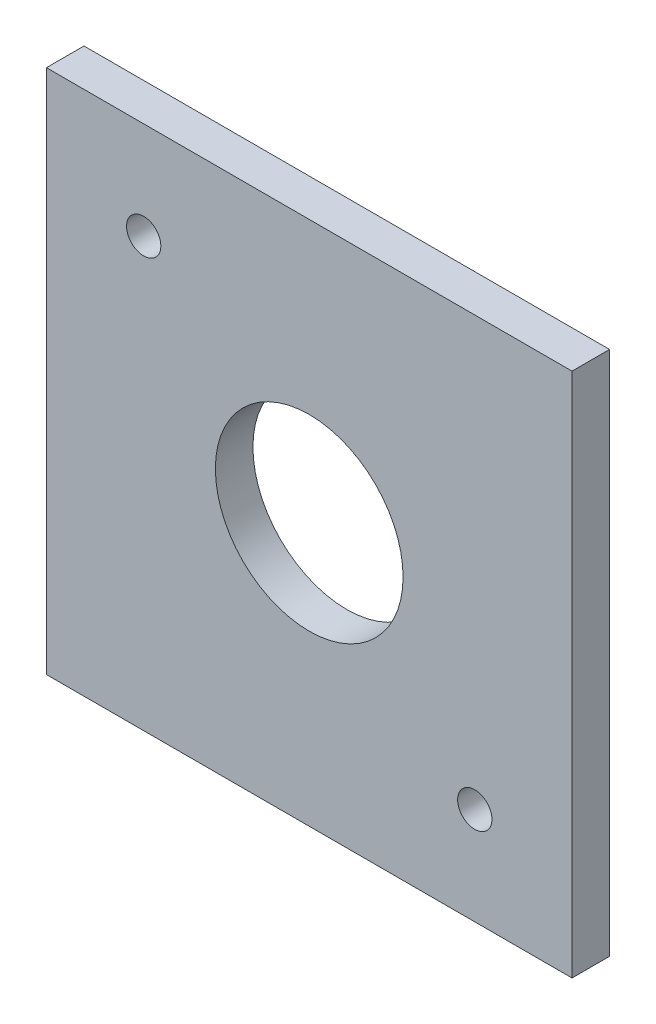
SolidWorks part; units mm, degrees
material "PET"
ref_plane "Front" through (0, 0, 0) normal (0, 0, 1) x (1, 0, 0)
ref_plane "Top" through (0, 0, 0) normal (0, 1, 0) x (1, 0, 0)
ref_plane "Right" through (0, 0, 0) normal (1, 0, 0) x (0, 0, -1)
sketch "Sketch1" plane through (0, 0, 0) normal (0, 0, 1) x (1, 0, 0)
  line L1 (-22.225, -22.225) -> (22.225, -22.225)
  line L2 (-22.225, -22.225) -> (-22.225, 22.225)
  line L3 (-22.225, 22.225) -> (22.225, 22.225)
  line L4 (22.225, -22.225) -> (22.225, 22.225)
  line L5 (-22.225, -22.225) -> (22.225, 22.225) construction
  line L6 (-22.225, 22.225) -> (22.225, -22.225) construction
  point P0 (0, 0)
  dimension "D1" = 44.45
extrude "Boss-Extrude1" add sketch "Sketch1" along normal blind 3.175
sketch "Sketch4" plane through (0, 0, 3.175) normal (0, 0, 1) x (1, 0, 0)
  line L0 (-14, 14) -> (14, 14) construction
  line L1 (14, 14) -> (14, -14) construction
  line L3 (14, -14) -> (-14, -14) construction
  line L4 (-14, -14) -> (-14, 14) construction
  line L6 (0, 14) -> (0, 22.225) construction
  line L7 (22.225, 22.225) -> (-22.225, 22.225) construction
  line L9 (14, 0) -> (22.225, 0) construction
  line L10 (22.225, -22.225) -> (22.225, 22.225) construction
  point P0 (-14, 14)
  point P2 (14, -14)
  dimension "D1" = 28
hole_wizard "M2.5 Clearance Hole1" positions "Sketch4" profile "Sketch3" hole size "M2.5" standard "ANSI Metric" end condition through all
sketch "Sketch3" plane through (-14, 14, 3.175) normal (1, 0, 0) x (0, -1, 0)
  line L0 (0, 0) -> (0, 3.175)
  line L1 (0, 3.175) -> (1.45, 3.175)
  line L2 (1.45, 3.175) -> (1.45, 0)
  line L5 (1.45, 0) -> (0, 0)
  line L11 (0, -6.35) -> (0, 107.95) construction
  dimension "Thru Hole Dia." = 2.9
  dimension "Thru Hole Depth" = 3.175
sketch "Sketch5" plane through (0, 0, 3.175) normal (0, 0, 1) x (1, 0, 0)
  circle A0 centre (0, 0) radius 7.9375
  dimension "D1" = 15.875
extrude "Cut-Extrude1" cut sketch "Sketch5" against normal through all
